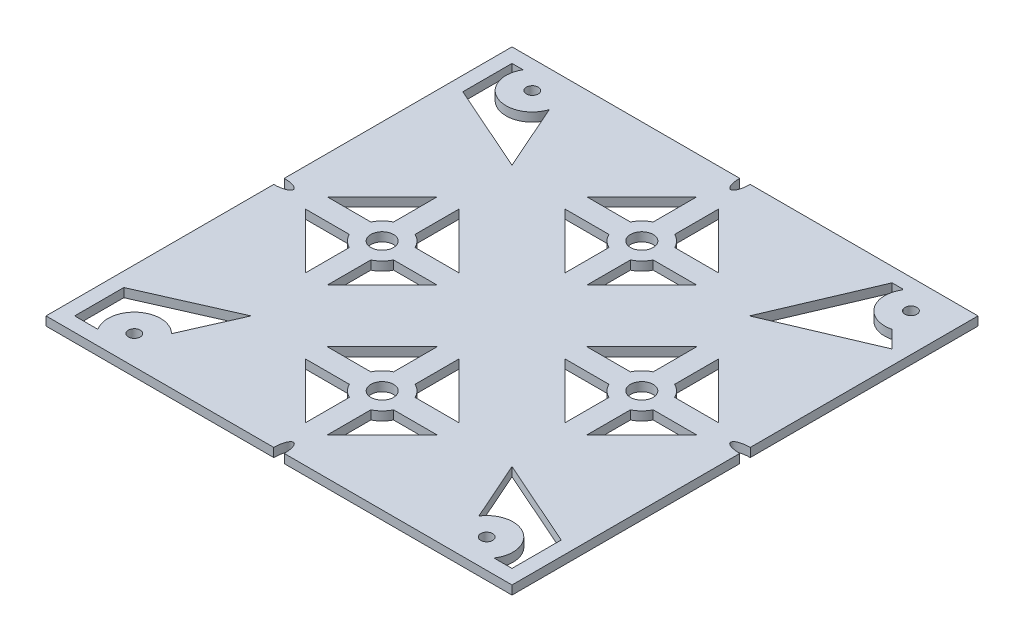
SolidWorks part; units mm, degrees
material "ABS"
ref_plane "Front Plane" through (0, 0, 0) normal (0, 0, 1) x (1, 0, 0)
ref_plane "Top Plane" through (0, 0, 0) normal (0, 1, 0) x (1, 0, 0)
ref_plane "Right Plane" through (0, 0, 0) normal (1, 0, 0) x (0, 0, -1)
sketch "Sketch1" plane through (0, 0, 0) normal (0, 1, 0) x (1, 0, 0)
  line L1 (0, 0) -> (97.6, 0)
  line L2 (0, 0) -> (0, 97.6)
  line L3 (0, 97.6) -> (97.6, 97.6)
  line L4 (97.6, 0) -> (97.6, 97.6)
  dimension "D1" = 97.6
  dimension "D2" = 97.6
extrude "Boss-Extrude1" add sketch "Sketch1" along normal blind 1.85
sketch "Sketch2" plane through (0, 0, 0) normal (0, -1, 0) x (-1, 0, 0)
  line L0 (-97.6, 97.6) -> (0, 0) construction
  line L1 (-97.6, 0) -> (0, 97.6) construction
  line L2 (-48.8, 97.6) -> (-48.8, 0) construction
  line L3 (-97.6, 97.6) -> (0, 97.6) construction
  line L4 (0, 0) -> (-97.6, 0) construction
  line L5 (-97.6, 48.8) -> (0, 48.8) construction
  line L6 (-97.6, 0) -> (-97.6, 97.6) construction
  line L7 (0, 97.6) -> (0, 0) construction
sketch "Sketch3" plane through (0, 0, 0) normal (0, -1, 0) x (1, 0, 0)
  line L0 (97.6, -97.6) -> (0, -97.6) construction
  line L1 (97.6, 0) -> (97.6, -97.6) construction
  line L2 (0, -97.6) -> (0, 0) construction
  line L3 (0, 0) -> (97.6, 0) construction
  line L4 (97.6, -94.6) -> (0, -94.6) construction
  line L5 (3, -97.6) -> (3, 0) construction
  line L6 (3, -94.6) -> (5.3161, -94.6)
  line L7 (3, -94.6) -> (3, -84.3)
  line L8 (3, -84.3) -> (21.4728, -76.1272)
  line L9 (97.6, 0) -> (0, -97.6) construction
  line L10 (21.4728, -76.1272) -> (13.3, -94.6)
  line L11 (21.4728, -21.4728) -> (13.3, -3)
  line L12 (3, -3) -> (13.3, -3)
  line L13 (0, -3) -> (97.6, -3) construction
  line L14 (3, -13.3) -> (3, -3)
  line L15 (3, -3) -> (7.8732, -3)
  line L16 (3, -13.3) -> (21.4728, -21.4728)
  line L17 (97.6, -97.6) -> (0, 0) construction
  line L18 (0, -97.6) -> (0, 0) construction
  line L19 (16.1614, -10.109) -> (21.4728, -21.4728) construction
  line L20 (94.6, -97.6) -> (94.6, 0) construction
  line L21 (94.6, -3) -> (94.6, -13.3)
  line L22 (94.6, -3) -> (84.3, -3)
  line L23 (94.6, -13.3) -> (76.1272, -21.4728)
  line L24 (76.1272, -21.4728) -> (84.3, -3)
  line L25 (94.6, -82.6) -> (73.6741, -73.6741)
  line L26 (73.6741, -73.6741) -> (82.6, -94.6)
  line L27 (94.6, -82.6) -> (82.6, -94.6) construction
  line L28 (94.6, -82.6) -> (91.0273, -86.1727)
  line L29 (82.6, -94.6) -> (85.1169, -94.6)
  line L30 (3, -94.6) -> (13.3, -94.6) construction
  circle A0 centre (89.66, -91.5) radius 1.25
  circle A1 centre (10.05, -91.8) radius 1.25
  circle A2 centre (12.45, -6.05) radius 1.25
  circle A3 centre (86.25, -6.05) radius 1.25
  circle A4 centre (89.66, -91.5) radius 5.5
  circle A5 centre (10.05, -91.8) radius 5.5
  circle A6 centre (12.45, -6.05) radius 5.5
  circle A7 centre (86.25, -6.05) radius 5.5
  dimension "D1" = 6.1
  dimension "D9" = 3
  dimension "D16" = 3
  dimension "D20" = 2.5
  dimension "D21" = 11
  dimension "D23" = 11
  dimension "D24" = 2.5
  dimension "D26" = 11
  dimension "D27" = 11
  dimension "D2" = 7.94
  dimension "D3" = 5.8
  dimension "D4" = 10.05
  dimension "D5" = 6.05
  dimension "D6" = 12.45
  dimension "D7" = 6.05
  dimension "D8" = 11.35
  dimension "D10" = 3
  dimension "D11" = 10.3
  dimension "D12" = 20.2
  dimension "D13" = 3
  dimension "D14" = 10.3
  dimension "D15" = 20.2
  dimension "D17" = 10.3
  dimension "D18" = 22.75
  dimension "D19" = 15
  dimension "D22" = 10.3
  dimension "D25" = 20.2
extrude "Cut-Extrude1" cut sketch "Sketch3" against normal blind 10
fillet "Fillet1" radius 0.2 1 edges at (85.1169, 0.925, -94.6)
sketch "Sketch5" plane through (0, 0, 0) normal (0, -1, 0) x (1, 0, 0)
  line L0 (78.0601, -69.3344) -> (24.4532, -15.7275) construction
  line L1 (15.9101, -24.6358) -> (67.2589, -75.9846) construction
  line L2 (97.6, -97.6) -> (0, 0) construction
  line L3 (25.594, -80.7317) -> (80.9701, -25.3556) construction
  line L4 (71.5743, -17.3) -> (16.8047, -72.0696) construction
  line L5 (97.6, 0) -> (0, -97.6) construction
  line L6 (51.05, -89.7671) -> (51.05, -80.6171)
  line L7 (46.55, -89.7671) -> (46.55, -80.6171)
  line L8 (48.8, -97.6) -> (48.8, 0) construction
  line L9 (51.05, -89.7671) -> (62.5825, -78.2346)
  line L10 (62.5825, -78.2346) -> (53.4325, -78.2346)
  line L11 (44.1675, -78.2346) -> (35.0175, -78.2346)
  line L12 (35.0175, -78.2346) -> (46.55, -89.7671)
  line L13 (48.8, -78.2346) -> (36.0473, -78.2346) construction
  line L14 (48.8, -73.7346) -> (36.0473, -73.7346) construction
  line L15 (44.1675, -73.7346) -> (35.0175, -73.7346)
  line L16 (46.55, -71.3521) -> (46.55, -62.2021)
  line L17 (53.4325, -73.7346) -> (62.5825, -73.7346)
  line L18 (51.05, -71.3521) -> (51.05, -62.2021)
  line L19 (62.5825, -73.7346) -> (51.05, -62.2021)
  line L20 (46.55, -62.2021) -> (35.0175, -73.7346)
  line L21 (48.8, -48.8) -> (-2.5605, -100.1605) construction
  line L22 (48.8, -48.8) -> (97.6, 0) construction
  line L23 (97.6, -97.6) -> (0, 0) construction
  line L24 (73.7346, -48.8) -> (73.7346, -36.0473) construction
  line L25 (78.2346, -48.8) -> (78.2346, -36.0473) construction
  line L26 (62.2021, -46.55) -> (73.7346, -35.0175)
  line L27 (73.7346, -62.5825) -> (62.2021, -51.05)
  line L28 (71.3521, -51.05) -> (62.2021, -51.05)
  line L29 (73.7346, -53.4325) -> (73.7346, -62.5825)
  line L30 (71.3521, -46.55) -> (62.2021, -46.55)
  line L31 (73.7346, -44.1675) -> (73.7346, -35.0175)
  line L32 (78.2346, -35.0175) -> (89.7671, -46.55)
  line L33 (78.2346, -44.1675) -> (78.2346, -35.0175)
  line L34 (78.2346, -62.5825) -> (78.2346, -53.4325)
  line L35 (89.7671, -51.05) -> (78.2346, -62.5825)
  line L36 (89.7671, -46.55) -> (80.6171, -46.55)
  line L37 (89.7671, -51.05) -> (80.6171, -51.05)
  line L38 (48.8, -19.3654) -> (61.5527, -19.3654) construction
  line L39 (48.8, -23.8654) -> (61.5527, -23.8654) construction
  line L40 (23.8654, -48.8) -> (23.8654, -61.5527) construction
  line L41 (19.3654, -48.8) -> (19.3654, -61.5527) construction
  line L42 (46.55, -7.8329) -> (46.55, -16.9829)
  line L43 (51.05, -7.8329) -> (51.05, -16.9829)
  line L44 (46.55, -7.8329) -> (35.0175, -19.3654)
  line L45 (35.0175, -19.3654) -> (44.1675, -19.3654)
  line L46 (53.4325, -19.3654) -> (62.5825, -19.3654)
  line L47 (62.5825, -19.3654) -> (51.05, -7.8329)
  line L48 (53.4325, -23.8654) -> (62.5825, -23.8654)
  line L49 (51.05, -26.2479) -> (51.05, -35.3979)
  line L50 (44.1675, -23.8654) -> (35.0175, -23.8654)
  line L51 (46.55, -26.2479) -> (46.55, -35.3979)
  line L52 (35.0175, -23.8654) -> (46.55, -35.3979)
  line L53 (51.05, -35.3979) -> (62.5825, -23.8654)
  line L54 (35.3979, -51.05) -> (23.8654, -62.5825)
  line L55 (23.8654, -35.0175) -> (35.3979, -46.55)
  line L56 (26.2479, -46.55) -> (35.3979, -46.55)
  line L57 (23.8654, -44.1675) -> (23.8654, -35.0175)
  line L58 (26.2479, -51.05) -> (35.3979, -51.05)
  line L59 (23.8654, -53.4325) -> (23.8654, -62.5825)
  line L60 (19.3654, -62.5825) -> (7.8329, -51.05)
  line L61 (19.3654, -53.4325) -> (19.3654, -62.5825)
  line L62 (19.3654, -35.0175) -> (19.3654, -44.1675)
  line L63 (7.8329, -46.55) -> (19.3654, -35.0175)
  line L64 (7.8329, -51.05) -> (16.9829, -51.05)
  line L65 (7.8329, -46.55) -> (16.9829, -46.55)
  line L66 (49.9, -97.6) -> (47.7, -97.6)
  line L67 (97.6, -97.6) -> (0, -97.6) construction
  line L68 (97.6, -48.8) -> (97.6, -49.9)
  line L69 (97.6, 0) -> (97.6, -97.6) construction
  line L70 (97.6, -48.8) -> (97.6, -47.7)
  line L71 (0, -49.9) -> (0, -48.8)
  line L72 (0, -97.6) -> (0, 0) construction
  line L73 (0, -48.8) -> (0, -47.7)
  line L74 (48.8, 0) -> (49.9, 0)
  line L75 (0, 0) -> (97.6, 0) construction
  line L76 (48.8, 0) -> (47.7, 0)
  circle A0 centre (48.8, -75.9846) radius 2.375
  circle A1 centre (48.8, -75.9846) radius 5.15
  circle A2 centre (75.9846, -48.8) radius 5.15
  circle A3 centre (75.9846, -48.8) radius 2.375
  circle A4 centre (48.8, -21.6154) radius 2.375
  circle A5 centre (48.8, -21.6154) radius 5.15
  circle A6 centre (21.6154, -48.8) radius 5.15
  circle A7 centre (21.6154, -48.8) radius 2.375
  ellipse E0 centre (48.8, -97.6) end of major axis (48.8, -94.6046) minor radius 1.1
  ellipse E1 centre (97.6, -48.8) end of major axis (94.5962, -48.8) minor radius 1.1
  ellipse E2 centre (0, -48.8) end of major axis (3, -48.8) minor radius 1.1
  ellipse E3 centre (48.8, 0) end of major axis (48.8, -3) minor radius 1.1
  line M15 (0, 0) -> (0, -97.6)
  line M16 (0, -97.6) -> (97.6, -97.6)
  line M17 (97.6, -97.6) -> (97.6, 0)
  line M18 (97.6, 0) -> (0, 0)
  dimension "D5" = 9.15
  dimension "D7" = 4.75
  dimension "D8" = 10.3
  dimension "D1" = 6.17
  dimension "D2" = 6.17
  dimension "D3" = 6.17
  dimension "D4" = 6.17
  dimension "D6" = 2.25
  dimension "D9" = 2.25
  dimension "D10" = 1.1
  dimension "D11" = 1.1
  dimension "D12" = 1.1
  dimension "D13" = 3
  dimension "D14" = 2.25
  dimension "D15" = 2.25
  dimension "D16" = 3
extrude "Cut-Extrude2" cut sketch "Sketch5" against normal blind 10 contours A1 L6 L9 L10 | A1 L11 L12 L7 | A0 | A1 L17 L19 L18 | A1 L16 L20 L15 | L61 A6 L64 L60 | L58 A6 L59 L54 | L57 A6 L56 L55 | L65 A6 L62 L63 | A7 | A3 | L37 A2 L34 L35 | L29 A2 L28 L27 | L30 A2 L31 L26 | L33 A2 L36 L32 | A5 L42 L44 L45 | A5 L46 L47 L43 | A5 L49 L53 L48 | A5 L50 L52 L51 | E0 M16 | E3 M18 | E1 M17 | E2 M15 | A4
